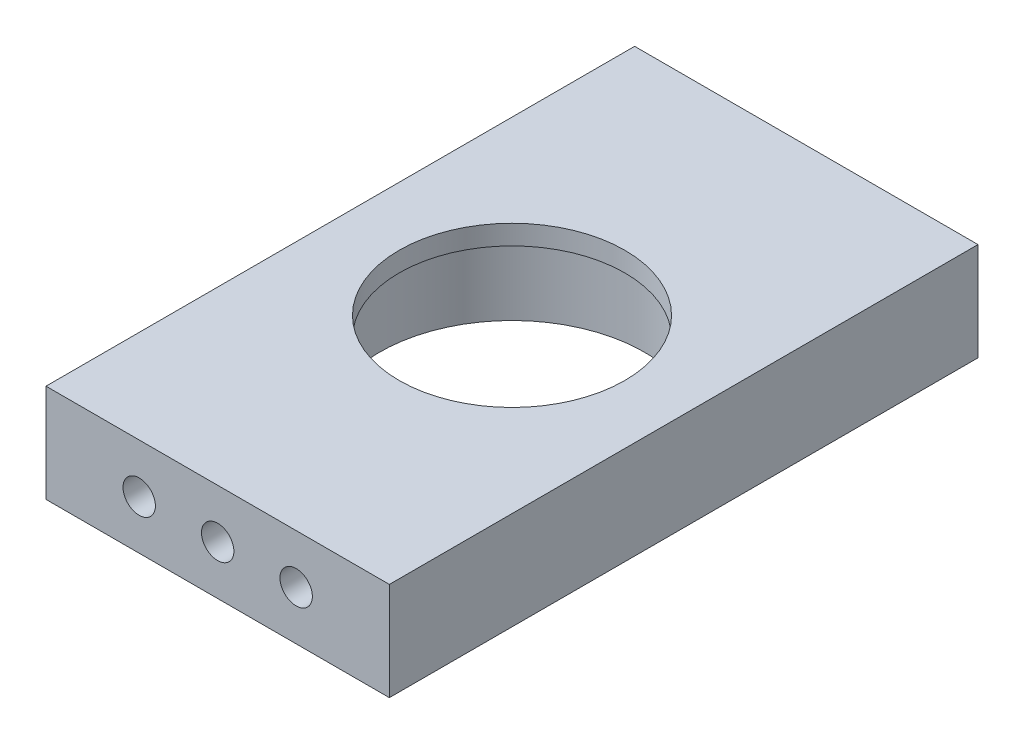
SolidWorks part; units mm, degrees
ref_plane "정면" through (0, 0, 0) normal (0, 0, 1) x (1, 0, 0)
ref_plane "윗면" through (0, 0, 0) normal (0, 1, 0) x (1, 0, 0)
ref_plane "우측면" through (0, 0, 0) normal (1, 0, 0) x (0, 0, -1)
sketch "스케치1" plane through (0, 0, 0) normal (0, 1, 0) x (1, 0, 0)
  line L9 (-17.5, 30) -> (17.5, 30)
  line L10 (-17.5, 30) -> (-17.5, -30)
  line L11 (-17.5, -30) -> (17.5, -30)
  line L12 (17.5, 30) -> (17.5, -30)
  line L13 (-17.5, 30) -> (17.5, -30) construction
  line L14 (-17.5, -30) -> (17.5, 30) construction
  circle A3 centre (0, 0) radius 13.5
  point P0 (0, 0)
  dimension "D1" = 27
  dimension "D2" = 35
  dimension "D3" = 60
extrude "보스-돌출1" add sketch "스케치1" along normal blind 10
sketch "스케치2" plane through (0, 0, 30) normal (0, 0, 1) x (1, 0, 0)
  line L0 (0, 0) -> (0, 50000) construction
  line L1 (0, 5) -> (50000, 5) construction
  line L2 (-17.5, 0) -> (17.5, 0) construction
  circle A0 centre (0, 5) radius 2
  circle A1 centre (-8, 5) radius 2
  circle A2 centre (8, 5) radius 2
  dimension "D2" = 4
  dimension "D3" = 4
  dimension "D4" = 4
  dimension "D1" = 5
  dimension "D5" = 8
  dimension "D6" = 8
sketch "스케치3" plane through (0, 10, 0) normal (0, 1, 0) x (1, 0, 0)
  circle A1 centre (0, 0) radius 11.5
  circle A2 centre (0, 0) radius 13.5
  circle A3 centre (0, 0) radius 13.5
  dimension "D1" = 0
  dimension "D2" = 2
extrude "보스-돌출2" add sketch "스케치3" against normal blind 2
sketch "스케치4" plane through (0, 0, -30) normal (0, 0, -1) x (-1, 0, 0)
  line L0 (-19.1388, 5) -> (49980.8612, 5) construction
  line L2 (0, 5) -> (0, 50005) construction
  line L4 (-17.5, 0) -> (17.5, 0) construction
  circle A0 centre (0, 5) radius 2
  circle A1 centre (8, 5) radius 2
  circle A2 centre (-8, 5) radius 2
  dimension "D2" = 4
  dimension "D3" = 4
  dimension "D4" = 4
  dimension "D1" = 5
hole_wizard "M4 나사 구멍2" positions "스케치7" profile "스케치8" tap size "M4" standard "ISO"
sketch "스케치7" plane through (0, 0, 30) normal (0, 0, 1) x (1, 0, 0)
  point P0 (-8, 5)
  point P3 (0, 5)
  point P6 (8, 5)
cosmetic thread "구멍 나사산4" parameters "D2"=4
cosmetic thread "구멍 나사산5" parameters "D2"=4
cosmetic thread "구멍 나사산6" parameters "D2"=4
sketch "스케치8" plane through (-8, 5, 30) normal (1, 0, 0) x (0, -1, 0)
  line L0 (0, 0) -> (0, 12.4914)
  line L1 (0, 12.4914) -> (1.65, 11.5)
  line L2 (1.65, 11.5) -> (1.65, 0)
  line L5 (1.65, 0) -> (0, 0)
  line L10 (0, 12.4914) -> (-1.65, 11.5) construction
  line L11 (0, -6.35) -> (0, 107.95) construction
  dimension "탭 드릴 지름" = 3.3
  dimension "탭 드릴 깊이" = 11.5
  dimension "드릴 각도" = 118
hole_wizard "M4 나사 구멍3" positions "스케치9" profile "스케치10" tap size "M4" standard "ISO"
sketch "스케치9" plane through (0, 0, -30) normal (0, 0, -1) x (-1, 0, 0)
  point P0 (-8, 5)
  point P3 (0, 5)
  point P6 (8, 5)
sketch "스케치10" plane through (8, 5, -30) normal (1, 0, 0) x (0, 1, 0)
  line L0 (0, 0) -> (0, 12.4914)
  line L1 (0, 12.4914) -> (1.65, 11.5)
  line L2 (1.65, 11.5) -> (1.65, 0)
  line L5 (1.65, 0) -> (0, 0)
  line L10 (0, 12.4914) -> (-1.65, 11.5) construction
  line L11 (0, -6.35) -> (0, 107.95) construction
  dimension "탭 드릴 지름" = 3.3
  dimension "탭 드릴 깊이" = 11.5
  dimension "드릴 각도" = 118
cosmetic thread "구멍 나사산7" parameters "D1"=8, "D2"=4
cosmetic thread "구멍 나사산8" parameters "D1"=8, "D2"=4
cosmetic thread "구멍 나사산9" parameters "D1"=8, "D2"=4
